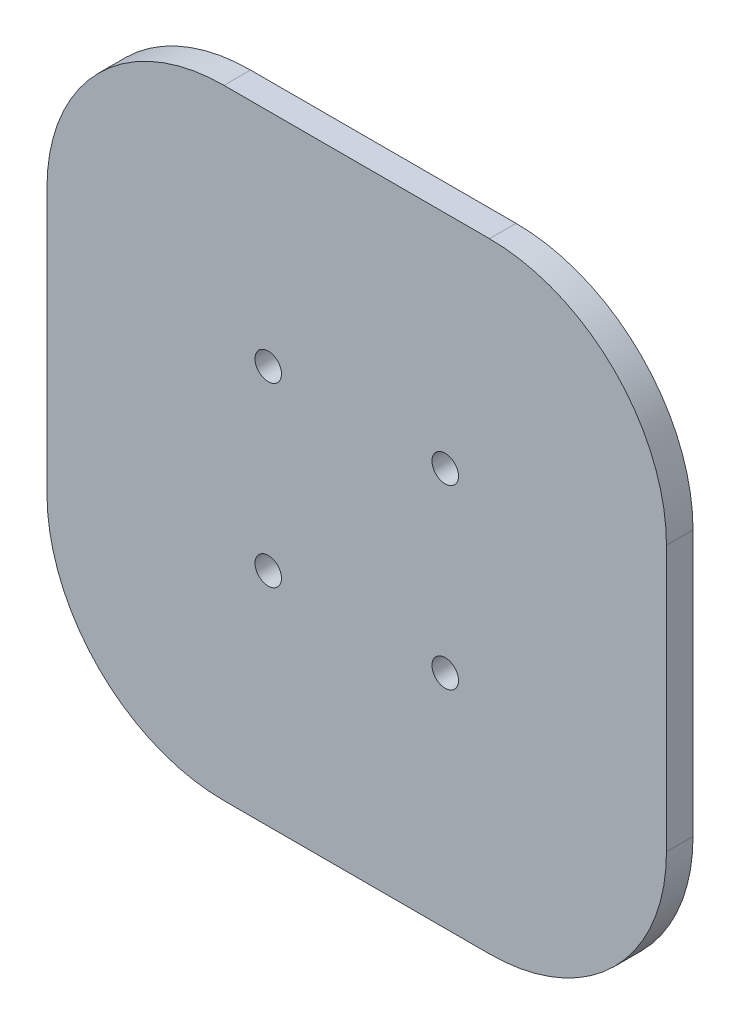
SolidWorks part; units mm, degrees
ref_plane "Ebene vorne" through (0, 0, 0) normal (0, 0, 1) x (1, 0, 0)
ref_plane "Ebene oben" through (0, 0, 0) normal (0, 1, 0) x (1, 0, 0)
ref_plane "Ebene rechts" through (0, 0, 0) normal (1, 0, 0) x (0, 0, -1)
sketch "Skizze1" plane through (0, 0, 0) normal (0, 0, 1) x (1, 0, 0)
  line L1 (-15, -35) -> (15, -35)
  line L2 (-35, -15) -> (-35, 15)
  line L3 (-15, 35) -> (15, 35)
  line L4 (35, -15) -> (35, 15)
  line L5 (-35, -35) -> (35, 35) construction
  line L6 (-35, 35) -> (35, -35) construction
  arc A0 (-15, -35) -> (-35, -15) centre (-15, -15) cw
  arc A1 (15, -35) -> (35, -15) centre (15, -15) ccw
  arc A2 (15, 35) -> (35, 15) centre (15, 15) cw
  arc A3 (-15, 35) -> (-35, 15) centre (-15, 15) ccw
  point P0 (0, 0)
  dimension "D1" = 20
  dimension "D2" = 70
  dimension "D3" = 70
extrude "Aufsatz-Linear austragen1" add sketch "Skizze1" along normal blind 3 contours L2 A3 L3 A2 L4 A1 L1 A0
sketch "Skizze2" plane through (0, 0, 3) normal (0, 0, 1) x (1, 0, 0)
  line L0 (0, 35) -> (0, -35) construction
  line L1 (-15, 35) -> (15, 35) construction
  line L2 (-15, -35) -> (15, -35) construction
  line L3 (-35, 0) -> (35, 0) construction
  line L4 (-35, -15) -> (-35, 15) construction
  line L5 (35, -15) -> (35, 15) construction
  circle A0 centre (-10, 10) radius 1.5
  circle A1 centre (10, 10) radius 1.5
  circle A2 centre (10, -10) radius 1.5
  circle A3 centre (-10, -10) radius 1.5
  dimension "D1" = 3
  dimension "D2" = 10
  dimension "D3" = 10
extrude "Schnitt-Linear austragen1" cut sketch "Skizze2" against normal up to next
